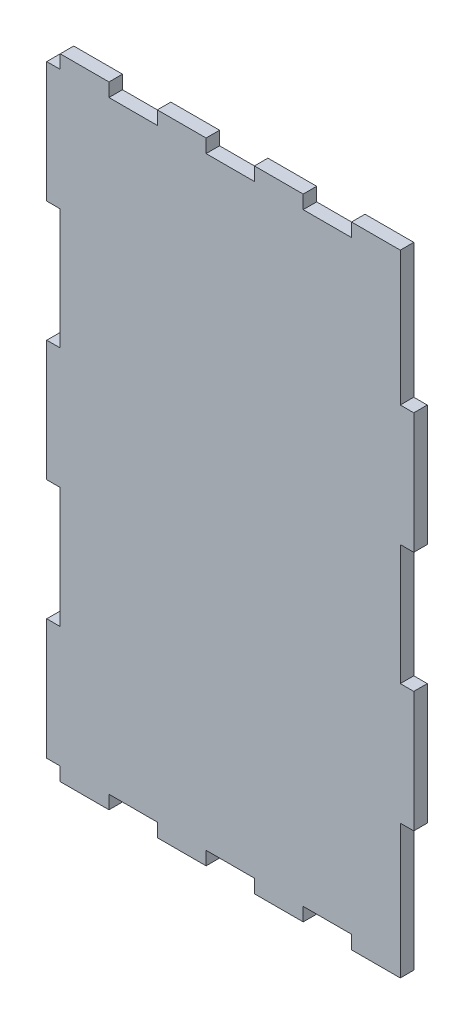
SolidWorks part; units mm, degrees
ref_plane "Front Plane" through (0, 0, 0) normal (0, 0, 1) x (1, 0, 0)
ref_plane "Top Plane" through (0, 0, 0) normal (0, 1, 0) x (1, 0, 0)
ref_plane "Right Plane" through (0, 0, 0) normal (1, 0, 0) x (0, 0, -1)
sketch "Sketch1" plane through (0, 0, 0) normal (0, 0, 1) x (1, 0, 0)
  line L0 (29.1375, 120.6625) -> (29.1375, 126.0625)
  line L1 (-67.9875, -120.6625) -> (67.9875, -120.6625)
  line L2 (-67.9875, -120.6625) -> (-67.9875, 120.6625)
  line L3 (-67.9875, 120.6625) -> (67.9875, 120.6625)
  line L4 (67.9875, -120.6625) -> (67.9875, 120.6625)
  line L5 (-67.9875, -120.6625) -> (67.9875, 120.6625) construction
  line L6 (-67.9875, 120.6625) -> (67.9875, -120.6625) construction
  line L7 (67.9875, -72.3975) -> (73.3875, -72.3975)
  line L8 (67.9875, -72.3975) -> (67.9875, -24.1325)
  line L9 (67.9875, -24.1325) -> (73.3875, -24.1325)
  line L10 (73.3875, -72.3975) -> (73.3875, -24.1325)
  line L11 (67.9875, 24.1325) -> (73.3875, 24.1325)
  line L12 (67.9875, 24.1325) -> (67.9875, 72.3975)
  line L13 (67.9875, 72.3975) -> (73.3875, 72.3975)
  line L14 (73.3875, 24.1325) -> (73.3875, 72.3975)
  line L15 (-67.9875, -120.6625) -> (-73.3875, -120.6625)
  line L16 (-67.9875, -120.6625) -> (-67.9875, -72.3975)
  line L17 (-67.9875, -72.3975) -> (-73.3875, -72.3975)
  line L18 (-73.3875, -120.6625) -> (-73.3875, -72.3975)
  line L19 (-67.9875, -24.1325) -> (-73.3875, -24.1325)
  line L20 (-67.9875, -24.1325) -> (-67.9875, 24.1325)
  line L21 (-67.9875, 24.1325) -> (-73.3875, 24.1325)
  line L22 (-73.3875, -24.1325) -> (-73.3875, 24.1325)
  line L23 (-67.9875, 72.3975) -> (-73.3875, 72.3975)
  line L24 (-67.9875, 72.3975) -> (-67.9875, 120.6625)
  line L25 (-67.9875, 120.6625) -> (-73.3875, 120.6625)
  line L26 (-73.3875, 72.3975) -> (-73.3875, 120.6625)
  line L27 (67.9875, 120.6625) -> (48.5625, 120.6625)
  line L28 (67.9875, 120.6625) -> (67.9875, 126.0625)
  line L29 (67.9875, 126.0625) -> (48.5625, 126.0625)
  line L30 (48.5625, 120.6625) -> (48.5625, 126.0625)
  line L31 (29.1375, 126.0625) -> (9.7125, 126.0625)
  line L32 (9.7125, 120.6625) -> (9.7125, 126.0625)
  line L33 (-9.7125, 120.6625) -> (-9.7125, 126.0625)
  line L34 (-9.7125, 126.0625) -> (-29.1375, 126.0625)
  line L35 (-29.1375, 120.6625) -> (-29.1375, 126.0625)
  line L36 (-48.5625, 120.6625) -> (-48.5625, 126.0625)
  line L37 (-48.5625, 126.0625) -> (-67.9875, 126.0625)
  line L38 (-67.9875, 120.6625) -> (-67.9875, 126.0625)
  line L39 (-67.9875, 0) -> (67.9875, 0) construction
  line L40 (67.9875, -120.6625) -> (67.9875, -126.0625)
  line L41 (67.9875, -126.0625) -> (48.5625, -126.0625)
  line L42 (48.5625, -120.6625) -> (48.5625, -126.0625)
  line L43 (29.1375, -120.6625) -> (29.1375, -126.0625)
  line L44 (29.1375, -126.0625) -> (9.7125, -126.0625)
  line L45 (9.7125, -120.6625) -> (9.7125, -126.0625)
  line L46 (-9.7125, -120.6625) -> (-9.7125, -126.0625)
  line L47 (-9.7125, -126.0625) -> (-29.1375, -126.0625)
  line L48 (-29.1375, -120.6625) -> (-29.1375, -126.0625)
  line L49 (-48.5625, -120.6625) -> (-48.5625, -126.0625)
  line L50 (-48.5625, -126.0625) -> (-67.9875, -126.0625)
  line L51 (-67.9875, -120.6625) -> (-67.9875, -126.0625)
  point P0 (0, 0)
  point P55 (0, 0)
  point P56 (0, 0)
  dimension "D1" = 241.325
  dimension "D2" = 135.975
  dimension "D3" = 5.4
  dimension "D4" = 48.265
  dimension "D5" = 48.265
  dimension "D6" = 5.4
  dimension "D7" = 48.265
  dimension "D8" = 48.265
  dimension "D9" = 5.4
  dimension "D10" = 5.4
  dimension "D11" = 5.4
  dimension "D12" = 48.265
  dimension "D13" = 48.265
  dimension "D14" = 19.425
  dimension "D15" = 5.4
  dimension "D17" = 19.425
extrude "Boss-Extrude1" add sketch "Sketch1" along normal blind 5.4 contours L1 L4 L3 L2 | L30 L3 L28 L29 | L32 L3 L0 L31 | L35 L3 L33 L34 | L26 L23 L2 L25 | L38 L3 L36 L37 | L11 L14 L13 L4 | L22 L19 L2 L21 | L7 L10 L9 L4 | L18 L15 L2 L17 | L1 L51 L50 L49 | L1 L48 L47 L46 | L1 L45 L44 L43 | L1 L42 L41 L40
sketch "Sketch2" plane through (0, 0, 5.4) normal (0, 0, 1) x (1, 0, 0)
  line L96 (-48.5219, -120.7031) -> (-29.1781, -120.7031)
  line L97 (-29.1781, -120.7031) -> (-29.1781, -126.1031)
  line L98 (-29.1781, -126.1031) -> (-9.6719, -126.1031)
  line L99 (-9.6719, -126.1031) -> (-9.6719, -120.7031)
  line L100 (-9.6719, -120.7031) -> (9.6719, -120.7031)
  line L101 (9.6719, -120.7031) -> (9.6719, -126.1031)
  line L102 (9.6719, -126.1031) -> (29.1781, -126.1031)
  line L103 (29.1781, -126.1031) -> (29.1781, -120.7031)
  line L104 (29.1781, -120.7031) -> (48.5219, -120.7031)
  line L105 (48.5219, -120.7031) -> (48.5219, -126.1031)
  line L106 (48.5219, -126.1031) -> (68.0281, -126.1031)
  line L107 (68.0281, -126.1031) -> (68.0281, -72.4381)
  line L108 (68.0281, -72.4381) -> (73.4281, -72.4381)
  line L109 (73.4281, -72.4381) -> (73.4281, -24.0919)
  line L110 (73.4281, -24.0919) -> (68.0281, -24.0919)
  line L111 (68.0281, -24.0919) -> (68.0281, 24.0919)
  line L112 (68.0281, 24.0919) -> (73.4281, 24.0919)
  line L113 (73.4281, 24.0919) -> (73.4281, 72.4381)
  line L114 (73.4281, 72.4381) -> (68.0281, 72.4381)
  line L115 (68.0281, 72.4381) -> (68.0281, 126.1031)
  line L116 (68.0281, 126.1031) -> (48.5219, 126.1031)
  line L117 (48.5219, 126.1031) -> (48.5219, 120.7031)
  line L118 (48.5219, 120.7031) -> (29.1781, 120.7031)
  line L119 (29.1781, 120.7031) -> (29.1781, 126.1031)
  line L120 (29.1781, 126.1031) -> (9.6719, 126.1031)
  line L121 (9.6719, 126.1031) -> (9.6719, 120.7031)
  line L122 (9.6719, 120.7031) -> (-9.6719, 120.7031)
  line L123 (-9.6719, 120.7031) -> (-9.6719, 126.1031)
  line L124 (-9.6719, 126.1031) -> (-29.1781, 126.1031)
  line L125 (-29.1781, 126.1031) -> (-29.1781, 120.7031)
  line L126 (-29.1781, 120.7031) -> (-48.5219, 120.7031)
  line L127 (-48.5219, 120.7031) -> (-48.5219, 126.1031)
  line L128 (-48.5219, 126.1031) -> (-68.0281, 126.1031)
  line L129 (-68.0281, 126.1031) -> (-68.0281, 120.7031)
  line L130 (-68.0281, 120.7031) -> (-73.4281, 120.7031)
  line L131 (-73.4281, 120.7031) -> (-73.4281, 72.3569)
  line L132 (-73.4281, 72.3569) -> (-68.0281, 72.3569)
  line L133 (-68.0281, 72.3569) -> (-68.0281, 24.1731)
  line L134 (-68.0281, 24.1731) -> (-73.4281, 24.1731)
  line L135 (-73.4281, 24.1731) -> (-73.4281, -24.1731)
  line L136 (-73.4281, -24.1731) -> (-68.0281, -24.1731)
  line L137 (-68.0281, -24.1731) -> (-68.0281, -72.3569)
  line L138 (-68.0281, -72.3569) -> (-73.4281, -72.3569)
  line L139 (-73.4281, -72.3569) -> (-73.4281, -120.7031)
  line L140 (-73.4281, -120.7031) -> (-68.0281, -120.7031)
  line L141 (-68.0281, -120.7031) -> (-68.0281, -126.1031)
  line L142 (-68.0281, -126.1031) -> (-48.5219, -126.1031)
  line L143 (-48.5219, -126.1031) -> (-48.5219, -120.7031)
  line L144 (-48.5219, -120.7031) -> (-29.1781, -120.7031)
  line L145 (-29.1781, -120.7031) -> (-29.1781, -126.1031)
  line L146 (-29.1781, -126.1031) -> (-9.6719, -126.1031)
  line L147 (-9.6719, -126.1031) -> (-9.6719, -120.7031)
  line L148 (-9.6719, -120.7031) -> (9.6719, -120.7031)
  line L149 (9.6719, -120.7031) -> (9.6719, -126.1031)
  line L150 (9.6719, -126.1031) -> (29.1781, -126.1031)
  line L151 (29.1781, -126.1031) -> (29.1781, -120.7031)
  line L152 (29.1781, -120.7031) -> (48.5219, -120.7031)
  line L153 (48.5219, -120.7031) -> (48.5219, -126.1031)
  line L154 (48.5219, -126.1031) -> (68.0281, -126.1031)
  line L155 (68.0281, -126.1031) -> (68.0281, -72.4381)
  line L156 (68.0281, -72.4381) -> (73.4281, -72.4381)
  line L157 (73.4281, -72.4381) -> (73.4281, -24.0919)
  line L158 (73.4281, -24.0919) -> (68.0281, -24.0919)
  line L159 (68.0281, -24.0919) -> (68.0281, 24.0919)
  line L160 (68.0281, 24.0919) -> (73.4281, 24.0919)
  line L161 (73.4281, 24.0919) -> (73.4281, 72.4381)
  line L162 (73.4281, 72.4381) -> (68.0281, 72.4381)
  line L163 (68.0281, 72.4381) -> (68.0281, 126.1031)
  line L164 (68.0281, 126.1031) -> (48.5219, 126.1031)
  line L165 (48.5219, 126.1031) -> (48.5219, 120.7031)
  line L166 (48.5219, 120.7031) -> (29.1781, 120.7031)
  line L167 (29.1781, 120.7031) -> (29.1781, 126.1031)
  line L168 (29.1781, 126.1031) -> (9.6719, 126.1031)
  line L169 (9.6719, 126.1031) -> (9.6719, 120.7031)
  line L170 (9.6719, 120.7031) -> (-9.6719, 120.7031)
  line L171 (-9.6719, 120.7031) -> (-9.6719, 126.1031)
  line L172 (-9.6719, 126.1031) -> (-29.1781, 126.1031)
  line L173 (-29.1781, 126.1031) -> (-29.1781, 120.7031)
  line L174 (-29.1781, 120.7031) -> (-48.5219, 120.7031)
  line L175 (-48.5219, 120.7031) -> (-48.5219, 126.1031)
  line L176 (-48.5219, 126.1031) -> (-68.0281, 126.1031)
  line L177 (-68.0281, 126.1031) -> (-68.0281, 120.7031)
  line L178 (-68.0281, 120.7031) -> (-73.4281, 120.7031)
  line L179 (-73.4281, 120.7031) -> (-73.4281, 72.3569)
  line L180 (-73.4281, 72.3569) -> (-68.0281, 72.3569)
  line L181 (-68.0281, 72.3569) -> (-68.0281, 24.1731)
  line L182 (-68.0281, 24.1731) -> (-73.4281, 24.1731)
  line L183 (-73.4281, 24.1731) -> (-73.4281, -24.1731)
  line L184 (-73.4281, -24.1731) -> (-68.0281, -24.1731)
  line L185 (-68.0281, -24.1731) -> (-68.0281, -72.3569)
  line L186 (-68.0281, -72.3569) -> (-73.4281, -72.3569)
  line L187 (-73.4281, -72.3569) -> (-73.4281, -120.7031)
  line L188 (-73.4281, -120.7031) -> (-68.0281, -120.7031)
  line L189 (-68.0281, -120.7031) -> (-68.0281, -126.1031)
  line L190 (-68.0281, -126.1031) -> (-48.5219, -126.1031)
  line L191 (-48.5219, -126.1031) -> (-48.5219, -120.7031)
  dimension "D1" = 0.0406
extrude "Boss-Extrude2" add sketch "Sketch2" against normal up to surface (5.4 mm away) up to face at (-5.8906, 0, 0)
